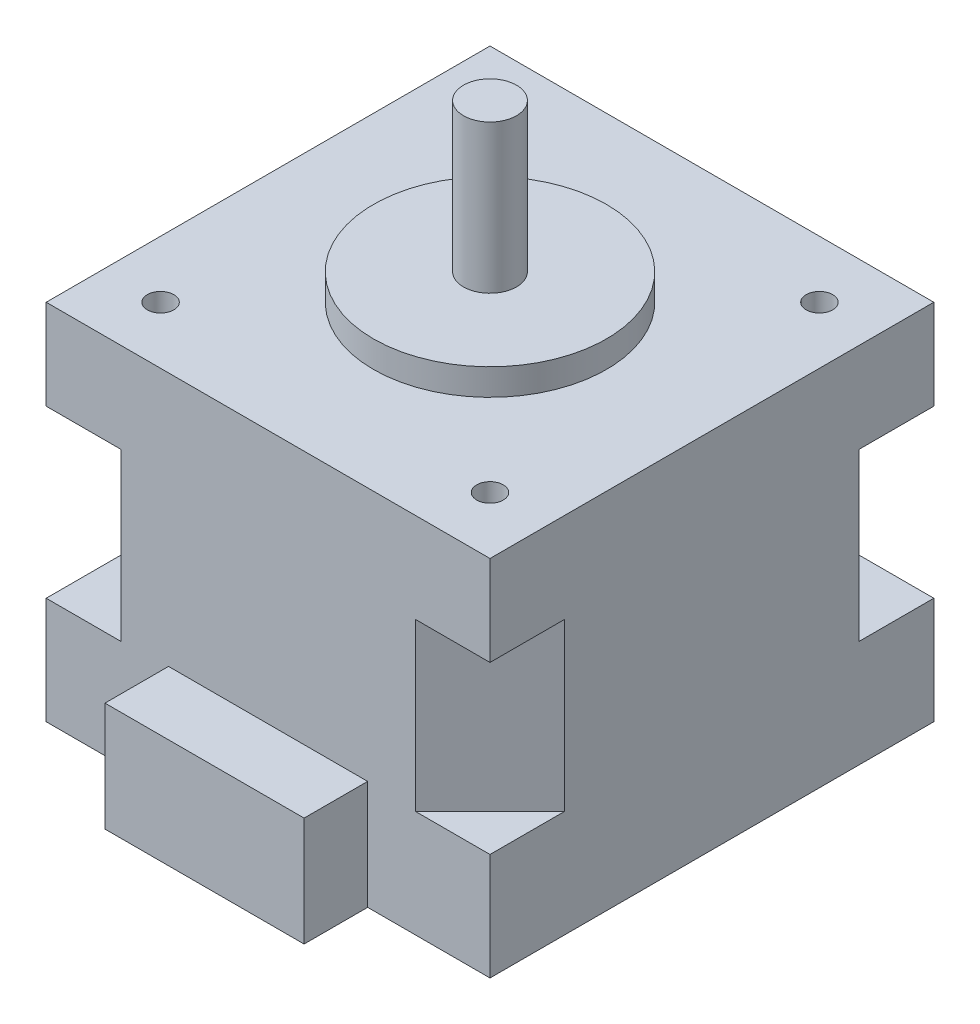
SolidWorks part; units mm, degrees
ref_plane "Front Plane" through (0, 0, 0) normal (0, 0, 1) x (1, 0, 0)
ref_plane "Top Plane" through (0, 0, 0) normal (0, 1, 0) x (1, 0, 0)
ref_plane "Right Plane" through (0, 0, 0) normal (1, 0, 0) x (0, 0, -1)
sketch "Sketch1" plane through (0, 0, 0) normal (0, 1, 0) x (1, 0, 0)
  line L1 (-20.95, 20.95) -> (20.95, 20.95)
  line L2 (-20.95, 20.95) -> (-20.95, -20.95)
  line L3 (-20.95, -20.95) -> (20.95, -20.95)
  line L4 (20.95, 20.95) -> (20.95, -20.95)
  line L5 (-20.95, 20.95) -> (20.95, -20.95) construction
  line L6 (-20.95, -20.95) -> (20.95, 20.95) construction
  point P0 (0, 0)
  dimension "D1" = 41.9
extrude "Boss-Extrude1" add sketch "Sketch1" along normal blind 34.3
sketch "Sketch2" plane through (0, 34.3, 0) normal (0, 1, 0) x (1, 0, 0)
  circle A0 centre (0, 0) radius 11
  dimension "D1" = 22
extrude "Boss-Extrude2" add sketch "Sketch2" along normal blind 2.5
sketch "Sketch3" plane through (0, 36.8, 0) normal (0, 1, 0) x (1, 0, 0)
  circle A0 centre (0, 0) radius 2.5
  dimension "D1" = 5
extrude "Boss-Extrude3" add sketch "Sketch3" along normal blind 14
sketch "Sketch4" plane through (0, 34.3, 0) normal (0, 1, 0) x (1, 0, 0)
  line L0 (20.95, 20.95) -> (-20.95, 20.95) construction
  line L1 (20.95, -20.95) -> (20.95, 20.95) construction
  circle A0 centre (15.55, 15.55) radius 1.25
  dimension "D1" = 2.5
  dimension "D2" = 5.4
  dimension "D3" = 5.4
extrude "Cut-Extrude1" cut sketch "Sketch4" against normal blind 7.9
mirror "Mirror1" about plane through (0, 0, 0) normal (1, 0, 0) of "Cut-Extrude1"
mirror "Mirror2" about plane through (0, 0, 0) normal (0, 0, 1) of "Mirror1", "Cut-Extrude1"
sketch "Sketch8" plane through (0, 0, -20.95) normal (0, 0, -1) x (-1, 0, 0)
  line L0 (20.95, 34.3) -> (20.95, 25.8)
  line L1 (20.95, 34.3) -> (20.95, 0) construction
  line L2 (20.95, 25.8) -> (-20.95, 25.8)
  line L3 (-20.95, 34.3) -> (-20.95, 0) construction
  dimension "D1" = 8.5
sketch "Sketch9" plane through (-20.95, 0, 0) normal (-1, 0, 0) x (0, 0, 1)
  line L0 (-20.95, 25.8) -> (20.95, 25.8)
  line L1 (-20.95, 34.3) -> (-20.95, 25.8) construction
  line L2 (20.95, 34.3) -> (20.95, 0) construction
ref_plane "Plane2" through (0, 25.8, 0) normal (0, -1, 0) x (-1, 0, 0)
sketch "Sketch10" plane through (0, 25.8, 0) normal (0, -1, 0) x (-1, 0, 0)
  line L0 (0, 20.95) -> (-13.9, 20.95)
  line L1 (20.95, 20.95) -> (-20.95, 20.95) construction
  line L2 (-20.95, 0) -> (-20.95, 13.9)
  line L3 (-20.95, -20.95) -> (-20.95, 20.95) construction
  line L4 (-20.95, 13.9) -> (-13.9, 20.95)
  line L5 (-13.9, 20.95) -> (-20.95, 20.95)
  line L6 (-20.95, 20.95) -> (-20.95, 13.9)
  dimension "D1" = 13.9
  dimension "D2" = 13.9
extrude "Cut-Extrude2" cut sketch "Sketch10" along normal blind 15.7 contours L4 L5 L6
mirror "Mirror3" about plane through (0, 0, 0) normal (1, 0, 0) of "Cut-Extrude2"
mirror "Mirror4" about plane through (0, 0, 0) normal (0, 0, 1) of "Mirror3", "Cut-Extrude2"
sketch "Sketch11" plane through (0, 0, 0) normal (0, -1, 0) x (1, 0, 0)
  line L0 (0, 20.95) -> (9.4, 20.95)
  line L1 (-20.95, 20.95) -> (20.95, 20.95) construction
  line L2 (0, 20.95) -> (-9.4, 20.95)
  line L3 (-9.4, 20.95) -> (-9.4, 26.95)
  line L4 (-9.4, 26.95) -> (9.4, 26.95)
  line L5 (9.4, 26.95) -> (9.4, 20.95)
  dimension "D1" = 9.4
  dimension "D2" = 9.4
  dimension "D3" = 6
extrude "Boss-Extrude4" add sketch "Sketch11" against normal blind 10.3
sketch "Sketch12" plane through (0, 0, 0) normal (0, -1, 0) x (1, 0, 0)
  circle A0 centre (0, 0) radius 4
  dimension "D1" = 8
extrude "Cut-Extrude3" cut sketch "Sketch12" against normal blind 3
